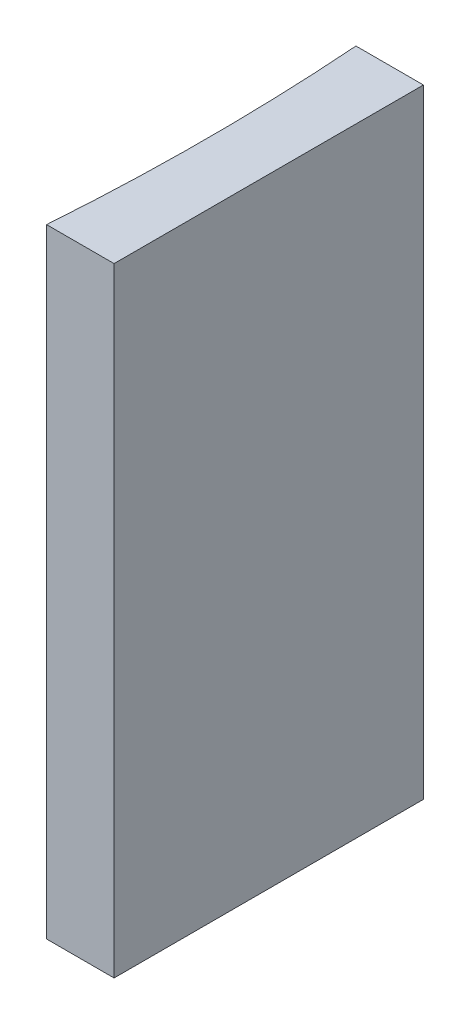
SolidWorks part; units mm, degrees
ref_plane "前视基准面" through (0, 0, 0) normal (0, 0, 1) x (1, 0, 0)
ref_plane "上视基准面" through (0, 0, 0) normal (0, 1, 0) x (1, 0, 0)
ref_plane "右视基准面" through (0, 0, 0) normal (1, 0, 0) x (0, 0, -1)
sketch "草图1" plane through (0, 0, 0) normal (0, 1, 0) x (1, 0, 0)
  line L0 (0, 0) -> (0, -10)
  line L1 (0, 0) -> (-2.182, 0)
  line L2 (0, -10) -> (-2.182, -10)
  line L3 (21.2259, -5) -> (-21.2259, -5) construction
  arc A0 (-2.182, -10) -> (-2.182, 0) centre (-70.78, -5) ccw
  point P7 (-2, -5)
  point P8 (0, -5)
  dimension "D2" = 68.78
  dimension "D3" = 2
  dimension "D1" = 10
extrude "凸台-拉伸1" add sketch "草图1" along normal blind 20
